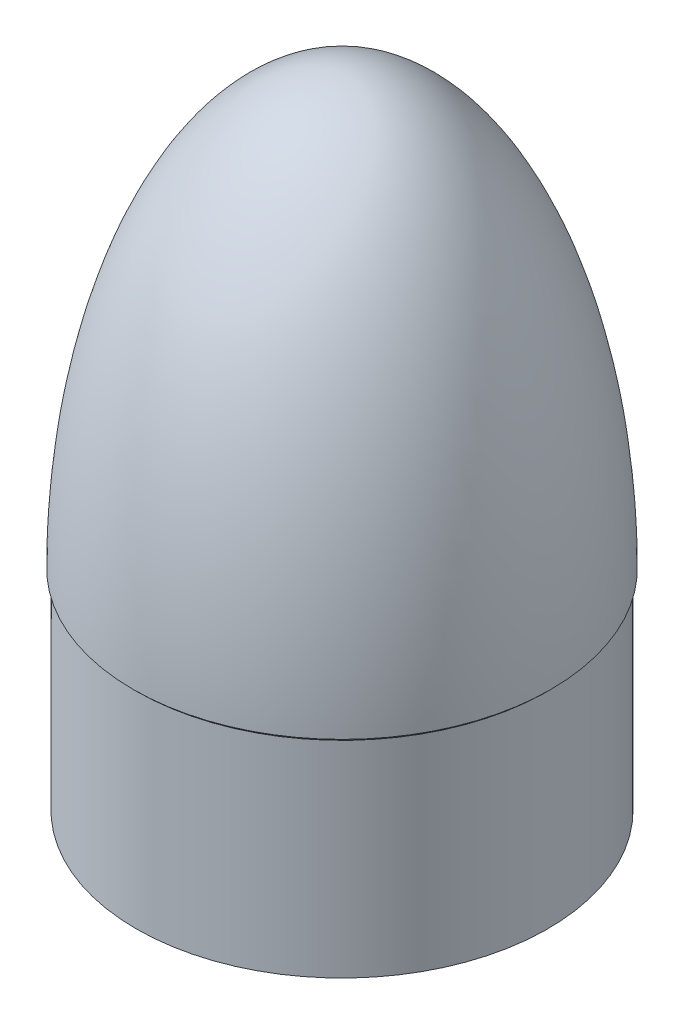
SolidWorks part; units mm, degrees
ref_plane "Front Plane" through (0, 0, 0) normal (0, 0, 1) x (1, 0, 0)
ref_plane "Top Plane" through (0, 0, 0) normal (0, 1, 0) x (1, 0, 0)
ref_plane "Right Plane" through (0, 0, 0) normal (1, 0, 0) x (0, 0, -1)
sketch "Sketch1" plane through (0, 0, 0) normal (0, 0, 1) x (1, 0, 0)
  line L3 (0, 0) -> (0, 202.3003) construction
  line L5 (0, 165.1) -> (0, 162.1028)
  line L12 (77.575, -80.518) -> (79.375, -80.518)
  line L13 (79.375, -80.518) -> (79.375, -1.143)
  line L14 (80.518, 0) -> (79.375, -1.143)
  line L15 (79.375, -1.143) -> (80.518, -1.143) construction
  line L17 (77.575, -0.3974) -> (77.575, -80.518)
  line L18 (77.575, -0.3974) -> (79.3153, 1.3429)
  line L19 (79.318, 0) -> (77.575, -1.743) construction
  ellipse E0 centre (0, 0) end of major axis (0, 162.1028) minor radius 79.318 (79.3153, 1.3429) -> (0, 162.1028) ccw
  ellipse E1 centre (0, 0) end of major axis (0, -165.1) minor radius 80.518 (80.518, 0) -> (0, 165.1) ccw
  dimension "D1" = 158.75
  dimension "D2" = 79.375
  dimension "D3" = 165.1
  dimension "D4" = 161.036
  dimension "D5" = 1.8
  dimension "D6" = 2.9972
  dimension "D7" = 45
  dimension "D8" = 1.2
  dimension "D9" = 1.8
revolve "Revolve1" add sketch "Sketch1" angle 360 about L5
